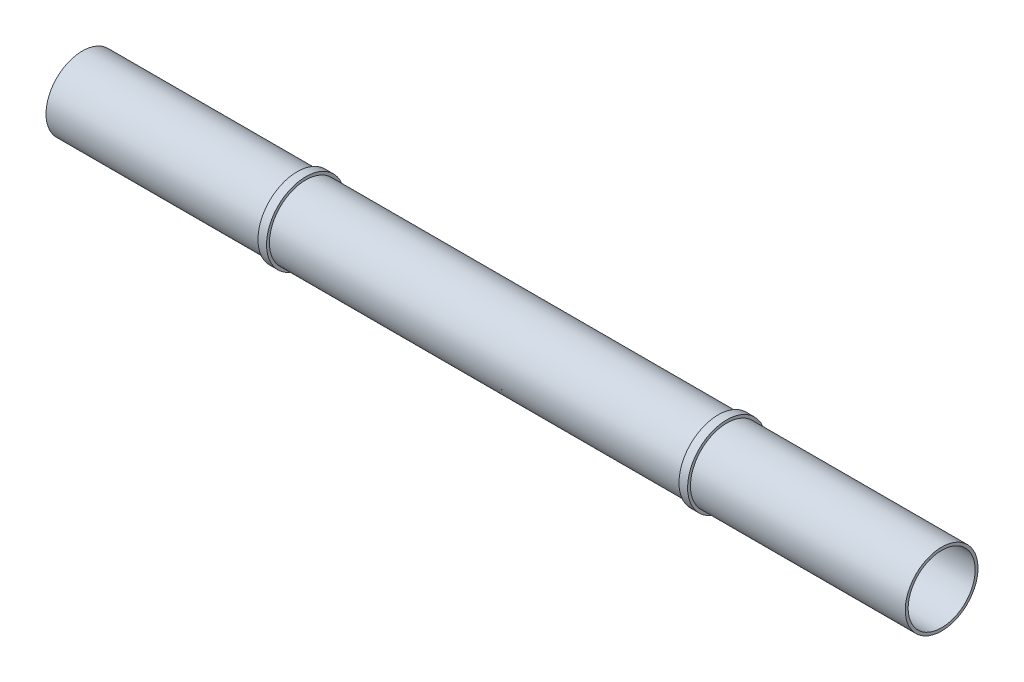
SolidWorks part; units mm, degrees
material "Alloy Steel"
ref_plane "Front Plane" through (0, 0, 0) normal (0, 0, 1) x (1, 0, 0)
ref_plane "Top Plane" through (0, 0, 0) normal (0, 1, 0) x (1, 0, 0)
ref_plane "Right Plane" through (0, 0, 0) normal (1, 0, 0) x (0, 0, -1)
sketch "Sketch1" plane through (0, 0, 0) normal (0, 0, 1) x (1, 0, 0)
  line L0 (-150, 0) -> (150, 0)
  line L1 (150, 0) -> (150, 12.7)
  line L2 (150, 12.7) -> (75, 12.7)
  line L3 (75, 12.7) -> (75, 13.7)
  line L4 (75, 13.7) -> (72, 13.7)
  line L5 (72, 13.7) -> (72, 12.7)
  line L6 (72, 12.7) -> (-72, 12.7)
  line L7 (0, 12.7) -> (0, 0) construction
  line L8 (-72, 13.7) -> (-72, 12.7)
  line L9 (-75, 13.7) -> (-72, 13.7)
  line L10 (-75, 12.7) -> (-75, 13.7)
  line L11 (-150, 12.7) -> (-75, 12.7)
  line L12 (-150, 0) -> (-150, 12.7)
  dimension "D1" = 12.7
  dimension "D2" = 3
  dimension "D3" = 1
  dimension "D4" = 75
  dimension "D5" = 150
revolve "Revolve1" add sketch "Sketch1" angle 360 about L0
sketch "Sketch3" plane through (150, 0, 0) normal (1, 0, 0) x (0, 0, -1)
  circle A0 centre (0, 0) radius 11.7
  circle A1 centre (0, 0) radius 12.7 construction
  dimension "D1" = 1
extrude "Cut-Extrude1" cut sketch "Sketch3" against normal through all both and the other way through all
